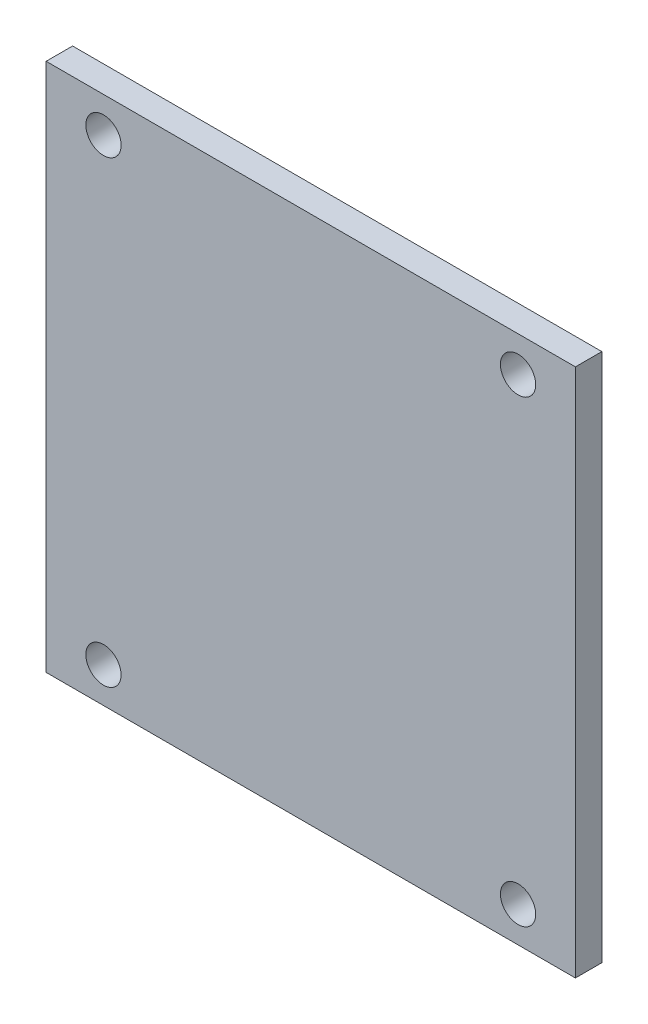
SolidWorks part; units mm, degrees
ref_plane "Front Plane" through (0, 0, 0) normal (0, 0, 1) x (1, 0, 0)
ref_plane "Top Plane" through (0, 0, 0) normal (0, 1, 0) x (1, 0, 0)
ref_plane "Right Plane" through (0, 0, 0) normal (1, 0, 0) x (0, 0, -1)
sketch "Sketch1" plane through (0, 0, 0) normal (0, 0, 1) x (1, 0, 0)
  line L1 (-30, -30) -> (30, -30)
  line L2 (-30, -30) -> (-30, 30)
  line L3 (-30, 30) -> (30, 30)
  line L4 (30, -30) -> (30, 30)
  line L5 (-30, -30) -> (30, 30) construction
  line L6 (-30, 30) -> (30, -30) construction
  point P0 (0, 0)
  dimension "D1" = 60
  dimension "D2" = 60
extrude "Boss-Extrude1" add sketch "Sketch1" along normal blind 3
sketch "Sketch2" plane through (0, 0, 0) normal (0, 0, 1) x (1, 0, 0)
  circle A0 centre (23.5, 26) radius 2
  circle A1 centre (-23.5, 26) radius 2
  circle A2 centre (-23.5, -26) radius 2
  circle A3 centre (23.5, -26) radius 2
  point P0 (0, 0)
  dimension "D5" = 4
  dimension "D6" = 4
  dimension "D7" = 4
  dimension "D8" = 4
extrude "Cut-Extrude1" cut sketch "Sketch2" along normal through all
